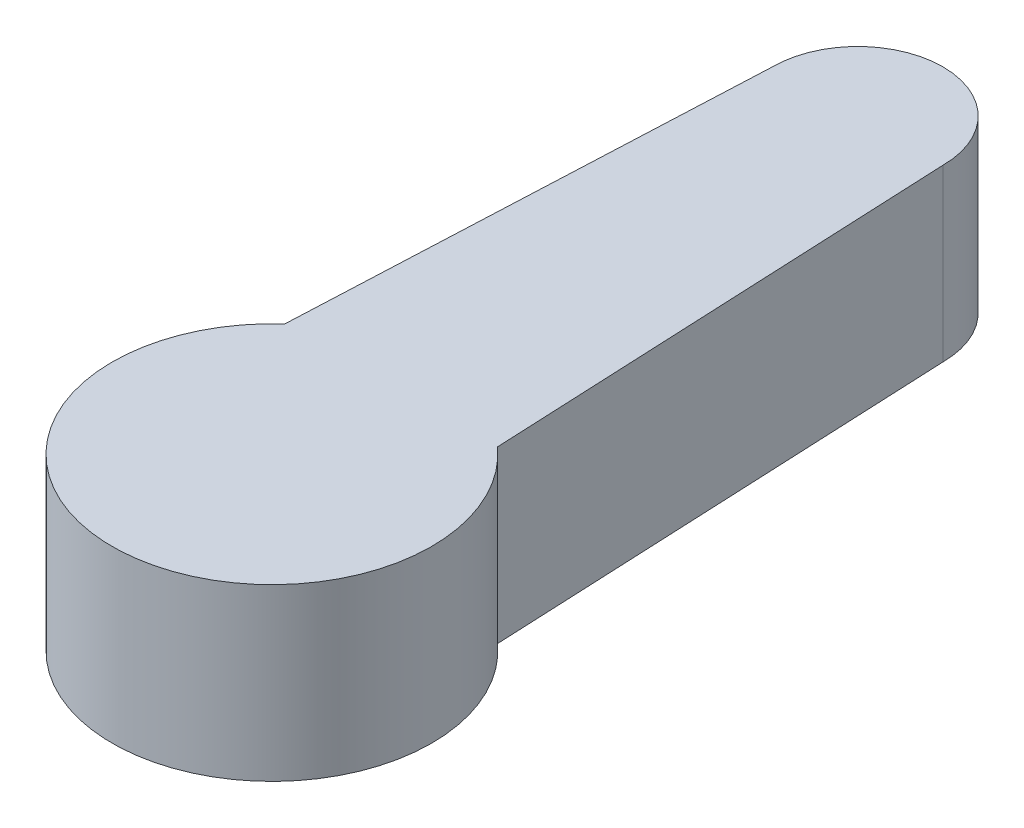
SolidWorks part; units mm, degrees
ref_plane "Front Plane" through (0, 0, 0) normal (0, 0, 1) x (1, 0, 0)
ref_plane "Top Plane" through (0, 0, 0) normal (0, 1, 0) x (1, 0, 0)
ref_plane "Right Plane" through (0, 0, 0) normal (1, 0, 0) x (0, 0, -1)
sketch "Sketch1" plane through (0, 0, 0) normal (0, 1, 0) x (1, 0, 0)
  line L0 (0, 0) -> (0, 40.844) construction
  line L1 (0, 0) -> (0, 13.75) construction
  line L2 (2.5, 2.75) -> (-2.5, 2.75) construction
  line L3 (-2, 13.75) -> (-2.5, 2.75)
  line L4 (2, 13.75) -> (2.5, 2.75)
  arc A0 (-2.4979, 2.797) -> (2.4979, 2.797) centre (0, 0) ccw
  arc A1 (2, 13.75) -> (-2, 13.75) centre (0, 13.75) ccw
  point P10 (0, 2.75)
  dimension "D1" = 7.5
  dimension "D2" = 4
  dimension "D3" = 13.75
  dimension "D4" = 5
  dimension "D5" = 2.75
extrude "Boss-Extrude1" add sketch "Sketch1" along normal blind 4
